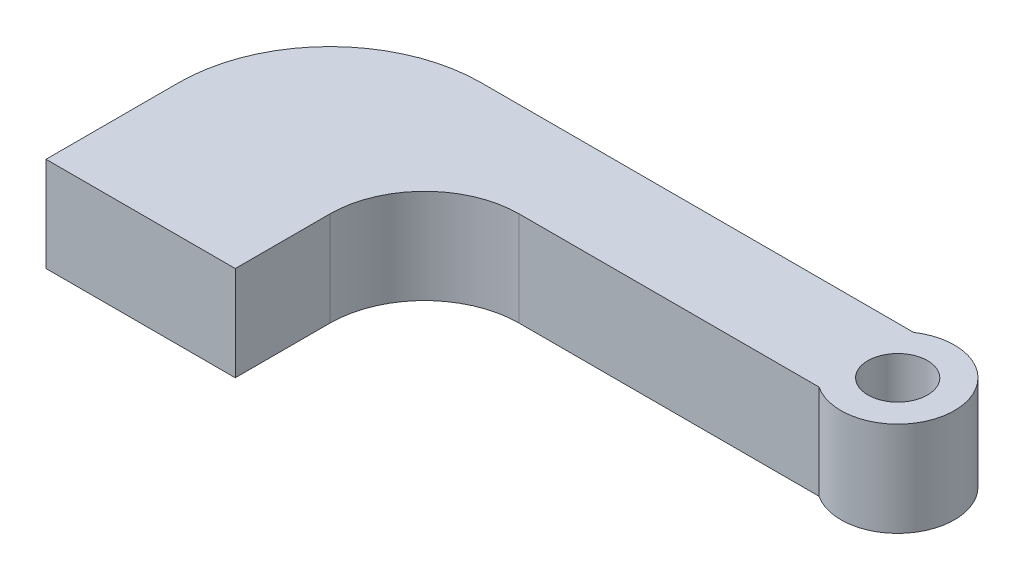
SolidWorks part; units mm, degrees
ref_plane "Front Plane" through (0, 0, 0) normal (0, 0, 1) x (1, 0, 0)
ref_plane "Top Plane" through (0, 0, 0) normal (0, 1, 0) x (1, 0, 0)
ref_plane "Right Plane" through (0, 0, 0) normal (1, 0, 0) x (0, 0, -1)
sketch "Sketch1" plane through (0, 0, 0) normal (0, 1, 0) x (1, 0, 0)
  line L0 (12.7, 0) -> (12.7, 6.35)
  line L1 (0, 0) -> (12.7, 0)
  line L2 (0, 0) -> (0, 8.89)
  line L3 (10.16, 19.05) -> (12.7, 19.05)
  line L4 (19.05, 12.7) -> (39.1688, 12.7)
  line L7 (12.7, 19.05) -> (39.1691, 19.05)
  line L8 (44.45, 13.7689) -> (44.45, 17.981) construction
  arc A0 (19.05, 12.7) -> (12.7, 6.35) centre (19.05, 6.35) ccw
  arc A1 (0, 8.89) -> (10.16, 19.05) centre (10.16, 8.89) cw
  circle A2 centre (41.275, 15.8749) radius 2
  arc A3 (39.1688, 12.7) -> (39.1691, 19.05) centre (41.275, 15.8749) ccw
  point P10 (12.7, 12.7)
  point P13 (0, 19.05)
  dimension "D5" = 6.35
  dimension "D6" = 10.16
  dimension "D7" = 4
  dimension "D9" = 7.62
  dimension "D1" = 19.05
  dimension "D2" = 12.7
  dimension "D3" = 12.7
  dimension "D4" = 31.75
  dimension "D8" = 3.175
extrude "Boss-Extrude1" add sketch "Sketch1" along normal blind 6.35
